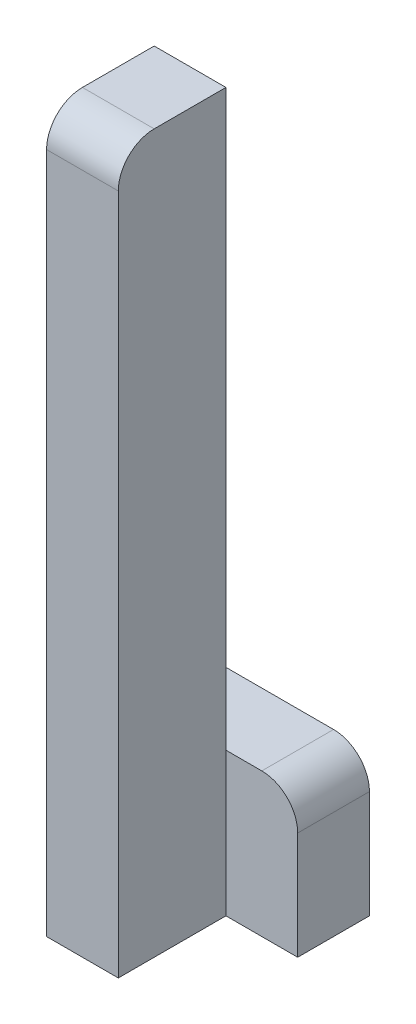
SolidWorks part; units mm, degrees
ref_plane "Front Plane" through (0, 0, 0) normal (0, 0, 1) x (1, 0, 0)
ref_plane "Top Plane" through (0, 0, 0) normal (0, 1, 0) x (1, 0, 0)
ref_plane "Right Plane" through (0, 0, 0) normal (1, 0, 0) x (0, 0, -1)
sketch "Sketch1" plane through (0, 0, 0) normal (0, 0, 1) x (1, 0, 0)
  line L1 (-30, -200) -> (-10, -200)
  line L2 (-10, -200) -> (-10, 0)
  line L3 (-10, 0) -> (-30, 0)
  line L4 (-30, 0) -> (-30, -200)
  dimension "D1" = 20
  dimension "Width" = 200
extrude "Boss-Extrude1" add sketch "Sketch1" along normal blind 30
sketch "Sketch2" plane through (0, 0, 0) normal (0, 0, 1) x (1, 0, 0)
  line L1 (-30, -200) -> (10, -200)
  line L2 (10, -200) -> (10, -160)
  line L3 (10, -160) -> (-30, -160)
  line L4 (-30, -160) -> (-30, -200)
  dimension "D1" = 40
  dimension "Width" = 40
extrude "Boss-Extrude2" add sketch "Sketch2" against normal blind 20
fillet "Fillet1" radius 10 2 edges at (10, -160, -10) (-20, 0, 30)
